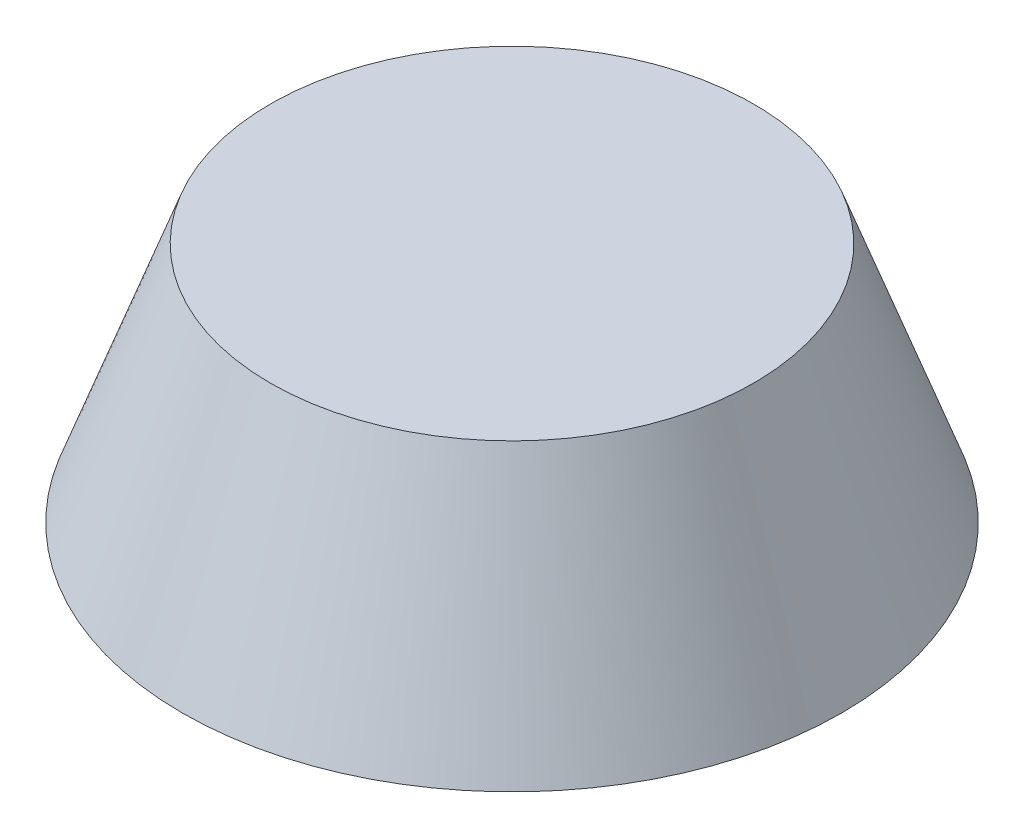
SolidWorks part; units mm, degrees
ref_plane "Front Plane" through (0, 0, 0) normal (0, 0, 1) x (1, 0, 0)
ref_plane "Top Plane" through (0, 0, 0) normal (0, 1, 0) x (1, 0, 0)
ref_plane "Right Plane" through (0, 0, 0) normal (1, 0, 0) x (0, 0, -1)
sketch "Sketch1" plane through (0, 0, 0) normal (0, 1, 0) x (1, 0, 0)
  circle A0 centre (0, 0) radius 3
  dimension "D1" = 6
extrude "Boss-Extrude1" add sketch "Sketch1" along normal blind 3
draft "Draft2" type of draft neutral plane draft angle 1 faces to draft 1 face at (0, 3, 3) neutral plane through (0, 3, 0) neutral plane normal (0, 1, 0) parameters "D1"=1
draft "Draft3" type of draft neutral plane draft angle 20 faces to draft 1 face at (0, 3, 3) neutral plane through (0, 3, 0) neutral plane normal (0, 1, 0) parameters "D1"=20
